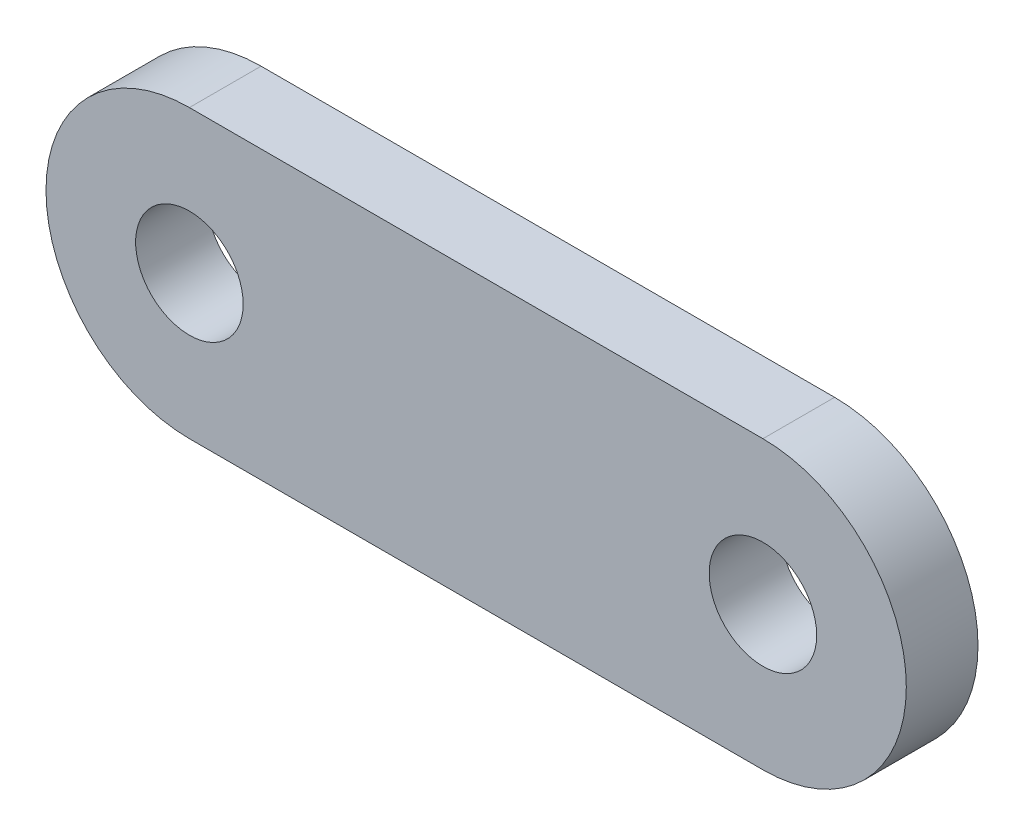
SolidWorks part; units mm, degrees
ref_plane "Front Plane" through (0, 0, 0) normal (0, 0, 1) x (1, 0, 0)
ref_plane "Top Plane" through (0, 0, 0) normal (0, 1, 0) x (1, 0, 0)
ref_plane "Right Plane" through (0, 0, 0) normal (1, 0, 0) x (0, 0, -1)
sketch "Sketch1" plane through (0, 0, 0) normal (0, 0, 1) x (1, 0, 0)
  line L0 (-25.4, 0) -> (25.4, 0) construction
  line L1 (-25.4, 12.7) -> (25.4, 12.7)
  line L2 (-25.4, -12.7) -> (25.4, -12.7)
  arc A0 (-25.4, 12.7) -> (-25.4, -12.7) centre (-25.4, 0) ccw
  arc A1 (25.4, -12.7) -> (25.4, 12.7) centre (25.4, 0) ccw
  circle A2 centre (-25.4, 0) radius 4.7625
  circle A3 centre (25.4, 0) radius 4.7625
  point P3 (0, 0)
  dimension "D1" = 9.525
  dimension "D2" = 50.8
  dimension "D3" = 25.4
extrude "Boss-Extrude1" add sketch "Sketch1" along normal blind 6.35
